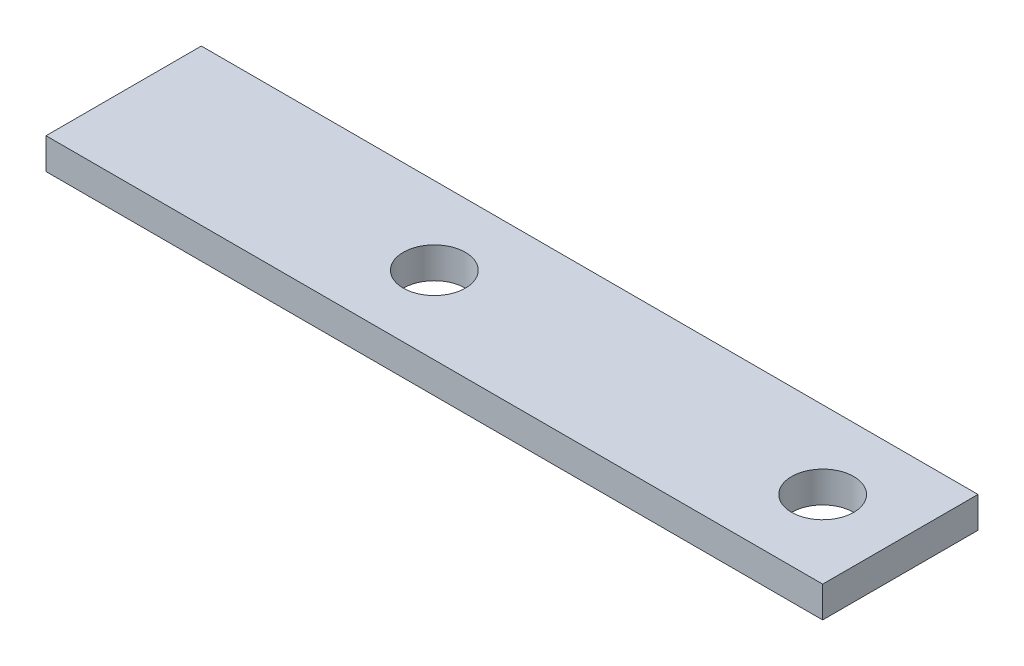
SolidWorks part; units mm, degrees
ref_plane "Спереди" through (0, 0, 0) normal (0, 0, 1) x (1, 0, 0)
ref_plane "Сверху" through (0, 0, 0) normal (0, 1, 0) x (1, 0, 0)
ref_plane "Справа" through (0, 0, 0) normal (1, 0, 0) x (0, 0, -1)
sketch "Эскиз1" plane through (0, 0, 0) normal (1, 0, 0) x (0, 0, -1)
  line L0 (0, 0) -> (20, 0)
extrude "Вытянуть-Тонкостенный1" add sketch "Эскиз1" along normal blind 100 thin
sketch "Эскиз2" plane through (0, 0, 0) normal (0, 1, 0) x (1, 0, 0)
  circle A0 centre (90, 10) radius 4
  circle A1 centre (40, 10) radius 4
  dimension "D1" = 2
extrude "Вырез-Вытянуть1" cut sketch "Эскиз2" against normal through all
